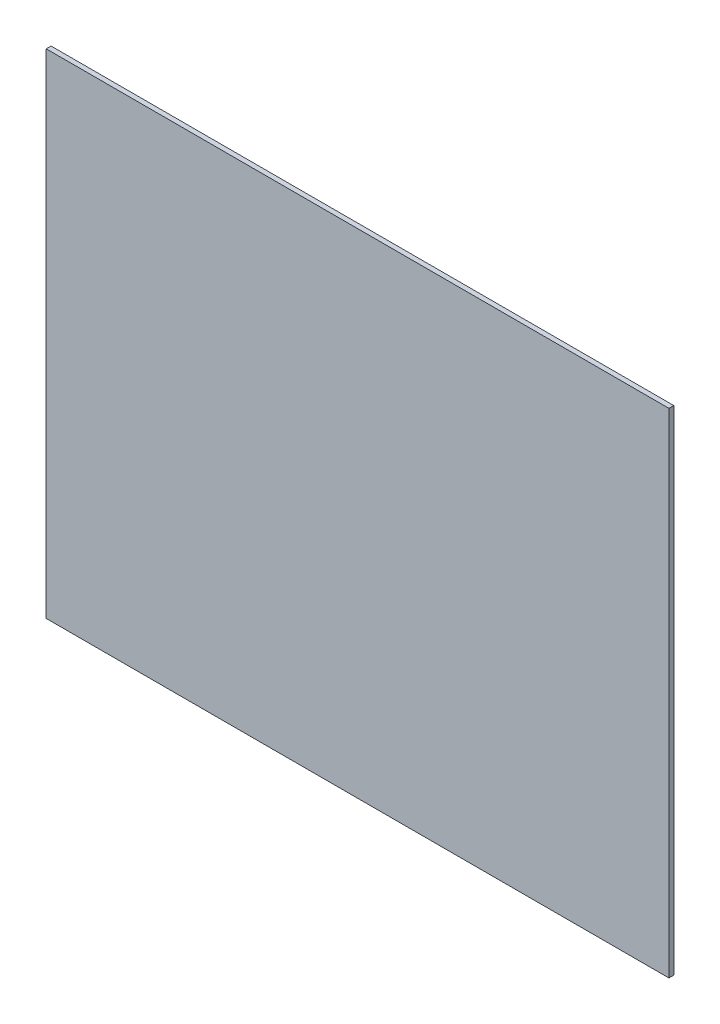
SolidWorks part; units mm, degrees
material "Acrílico (Impacto medio-alto)"
ref_plane "Alzado" through (0, 0, 0) normal (0, 0, 1) x (1, 0, 0)
ref_plane "Planta" through (0, 0, 0) normal (0, 1, 0) x (1, 0, 0)
ref_plane "Vista lateral" through (0, 0, 0) normal (1, 0, 0) x (0, 0, -1)
sketch "Croquis1" plane through (0, 0, 0) normal (0, 0, 1) x (1, 0, 0)
  line L1 (0, 0) -> (385, 0)
  line L2 (0, 0) -> (0, 305)
  line L3 (0, 305) -> (385, 305)
  line L4 (385, 0) -> (385, 305)
  dimension "D1" = 305
  dimension "D2" = 385
extrude "Saliente-Extruir1" add sketch "Croquis1" along normal blind 3
